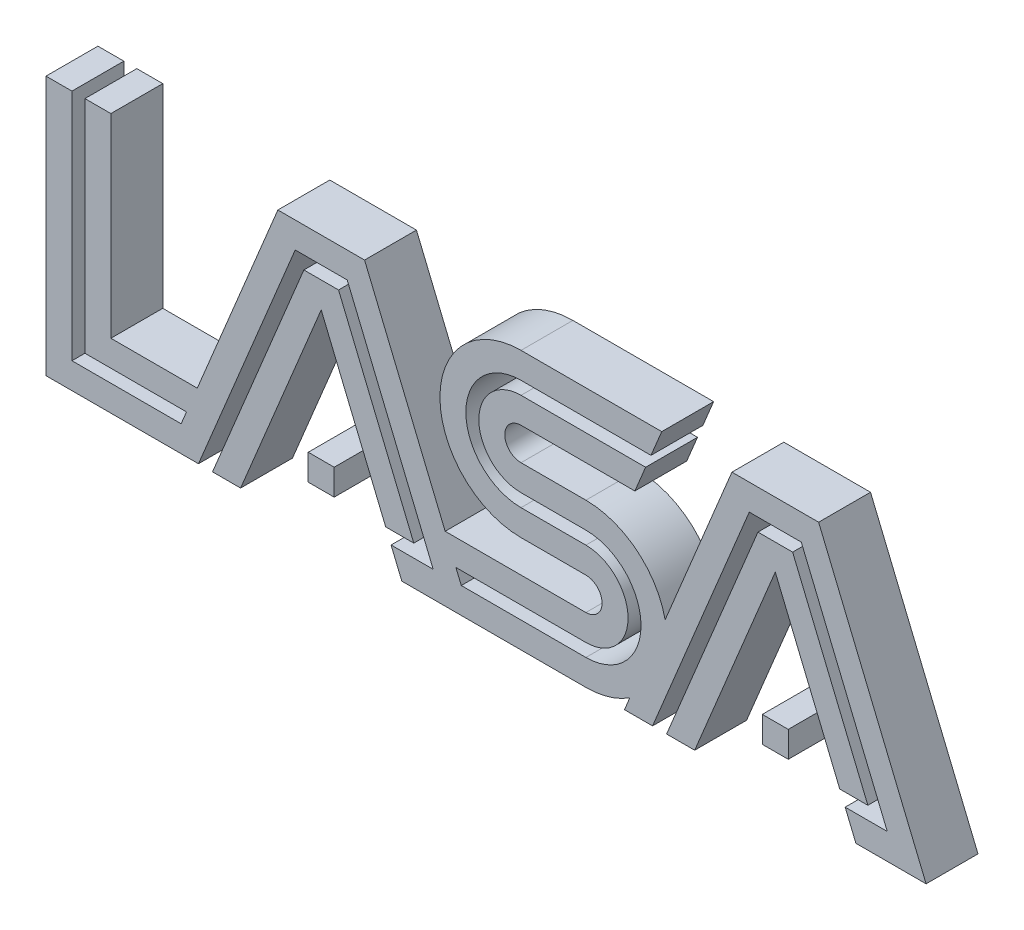
SolidWorks part; units mm, degrees
ref_plane "Front Plane" through (0, 0, 0) normal (0, 0, 1) x (1, 0, 0)
ref_plane "Top Plane" through (0, 0, 0) normal (0, 1, 0) x (1, 0, 0)
ref_plane "Right Plane" through (0, 0, 0) normal (1, 0, 0) x (0, 0, -1)
sketch "Sketch2" plane through (0, 0, 0) normal (0, 0, 1) x (1, 0, 0)
  line L0 (0, 0) -> (0, 100)
  line L1 (0, 100) -> (25, 100)
  line L2 (25, 100) -> (25, 25)
  line L3 (25, 25) -> (58.2955, 25)
  line L4 (0, 0) -> (75, 0)
  line L5 (25, 25) -> (25, 0) construction
  line L6 (58.2955, 25) -> (89.3616, 100)
  line L7 (89.3616, 100) -> (122.7705, 100)
  line L8 (122.7705, 100) -> (153.8365, 25)
  line L9 (75, 0) -> (106.066, 75)
  line L10 (106.066, 75) -> (137.132, 0)
  line L11 (58.2955, 25) -> (81.3925, 15.4329) construction
  line L12 (153.8365, 25) -> (130.7395, 15.4329) construction
  line L13 (106.066, 75) -> (106.066, 100) construction
  line L14 (137.132, 0) -> (208.0693, 0)
  line L15 (153.8365, 25) -> (208.0693, 25)
  line L16 (208.0693, 37.5) -> (183.0693, 37.5)
  line L17 (208.0693, 62.5) -> (183.0693, 62.5)
  line L18 (183.0693, 75) -> (226.9464, 75)
  line L19 (183.0693, 100) -> (237.3017, 100)
  line L20 (225.0062, 4.9878) -> (222.9402, 0)
  line L21 (222.9402, 0) -> (250, 0)
  line L22 (250, 0) -> (281.066, 75)
  line L23 (238.6157, 37.844) -> (264.3616, 100)
  line L24 (238.6157, 37.844) -> (261.7127, 28.2769) construction
  line L25 (142.6496, 52.0076) -> (154.1981, 56.7911) construction
  line L26 (264.3616, 100) -> (297.7705, 100)
  line L27 (281.066, 75) -> (281.066, 100) construction
  line L28 (281.066, 75) -> (312.132, 0)
  line L29 (312.132, 0) -> (339.1918, 0)
  line L30 (339.1918, 0) -> (297.7705, 100)
  line L31 (312.132, 0) -> (335.229, 9.5671) construction
  line L32 (183.0693, 75) -> (183.0693, 62.5) construction
  line L33 (237.3017, 100) -> (226.9464, 75)
  line L34 (226.9464, 75) -> (250.0434, 65.4329) construction
  line L35 (106.066, 75) -> (106.066, 20) construction
  line L36 (281.066, 75) -> (281.066, 20) construction
  line L37 (111.066, 15) -> (101.066, 15)
  line L38 (111.066, 15) -> (111.066, 25)
  line L39 (111.066, 25) -> (101.066, 25)
  line L40 (101.066, 15) -> (101.066, 25)
  line L41 (111.066, 15) -> (101.066, 25) construction
  line L42 (111.066, 25) -> (101.066, 15) construction
  line L44 (276.066, 15) -> (286.066, 15)
  line L45 (276.066, 15) -> (276.066, 25)
  line L46 (276.066, 25) -> (286.066, 25)
  line L47 (286.066, 15) -> (286.066, 25)
  line L48 (276.066, 15) -> (286.066, 25) construction
  line L49 (276.066, 25) -> (286.066, 15) construction
  arc A0 (208.0693, 25) -> (208.0693, 37.5) centre (208.0693, 31.25) ccw
  arc A1 (208.0693, 0) -> (208.0693, 62.5) centre (208.0693, 31.25) ccw construction
  arc A2 (183.0693, 62.5) -> (183.0693, 75) centre (183.0693, 68.75) cw
  arc A3 (183.0693, 37.5) -> (183.0693, 100) centre (183.0693, 68.75) cw
  arc A4 (208.0693, 0) -> (225.0062, 4.9878) centre (208.0693, 31.25) ccw
  arc A5 (208.0693, 62.5) -> (238.6157, 37.844) centre (208.0693, 31.25) cw
  dimension "D6" = 10
  dimension "D1" = 100
  dimension "D2" = 25
  dimension "D3" = 45
  dimension "D4" = 75
  dimension "D5" = 175
extrude "Boss-Extrude1" add sketch "Sketch2" along normal blind 20 contours L1 L2 L3 L6 L7 L8 L15 A0 L16 A3 L19 L33 L18 A2 L17 A5 L23 L26 L30 L29 L28 L22 L21 L20 A4 L14 L10 L9 L4 L0 | L37 L40 L39 L38 | L44 L47 L46 L45
sketch "Sketch5" plane through (0, 0, 20) normal (0, 0, 1) x (1, 0, 0)
  line L0 (10, 100) -> (10, 10)
  line L1 (0, 100) -> (25, 100) construction
  line L2 (10, 10) -> (52.0823, 10)
  line L3 (52.0823, 10) -> (54.1534, 15)
  line L4 (54.1534, 15) -> (15, 15)
  line L5 (15, 15) -> (15, 100)
  line L6 (15, 100) -> (10, 100)
  line L7 (0, 100) -> (10, 100) construction
  line L8 (15, 100) -> (25, 100) construction
  line L9 (25, 25) -> (25, 15) construction
  line L10 (25, 10) -> (25, 0) construction
  line L11 (0, 0) -> (75, 0) construction
  line L12 (58.2955, 25) -> (89.3616, 100) construction
  line L13 (64.1761, 0) -> (99.3842, 85)
  line L14 (99.3842, 85) -> (112.7478, 85)
  line L15 (112.7478, 85) -> (141.7428, 15)
  line L16 (141.7428, 15) -> (130.9188, 15)
  line L17 (106.066, 75) -> (137.132, 0) construction
  line L18 (130.9188, 15) -> (132.9899, 10)
  line L19 (132.9899, 10) -> (149.2258, 10)
  line L20 (149.2258, 10) -> (116.0887, 90)
  line L21 (116.0887, 90) -> (96.0433, 90)
  line L22 (96.0433, 90) -> (58.7641, 0)
  line L23 (58.7641, 0) -> (64.1761, 0)
  line L24 (122.7705, 100) -> (153.8365, 25) construction
  line L25 (96.0433, 90) -> (86.8045, 93.8268) construction
  line L26 (106.066, 90) -> (106.066, 100) construction
  line L27 (89.3616, 100) -> (122.7705, 100) construction
  line L28 (106.066, 75) -> (96.8272, 78.8268) construction
  line L29 (106.066, 75) -> (115.3048, 78.8268) construction
  line L30 (106.066, 85) -> (106.066, 75) construction
  line L31 (149.2258, 10) -> (149.2258, 0) construction
  line L32 (137.132, 0) -> (208.0693, 0) construction
  line L33 (141.7428, 15) -> (141.7428, 10) construction
  line L34 (231.0885, 85) -> (233.1596, 90)
  line L35 (237.3017, 100) -> (226.9464, 75) construction
  line L36 (233.1596, 90) -> (183.0693, 90)
  line L37 (231.0885, 85) -> (183.0693, 85)
  line L38 (183.0693, 52.5) -> (208.0693, 52.5)
  line L39 (183.0693, 47.5) -> (208.0693, 47.5)
  line L40 (208.0693, 15) -> (157.9786, 15)
  line L41 (157.9786, 15) -> (160.0497, 10)
  line L42 (160.0497, 10) -> (208.0693, 10)
  line L43 (239.1761, 0) -> (233.7641, 0)
  line L44 (222.9402, 0) -> (250, 0) construction
  line L45 (233.7641, 0) -> (271.0433, 90)
  line L46 (271.0433, 90) -> (291.0887, 90)
  line L47 (291.0887, 90) -> (324.2258, 10)
  line L48 (324.2258, 10) -> (307.9899, 10)
  line L49 (281.066, 75) -> (312.132, 0) construction
  line L50 (307.9899, 10) -> (305.9188, 15)
  line L51 (305.9188, 15) -> (316.7428, 15)
  line L52 (316.7428, 15) -> (287.7478, 85)
  line L53 (287.7478, 85) -> (274.3842, 85)
  line L54 (274.3842, 85) -> (239.1761, 0)
  line L56 (250, 0) -> (281.066, 75) construction
  line L57 (281.066, 90) -> (281.066, 100) construction
  line L58 (264.3616, 100) -> (297.7705, 100) construction
  line L59 (281.066, 85) -> (281.066, 90) construction
  arc A0 (183.0693, 85) -> (183.0693, 52.5) centre (183.0693, 68.75) ccw
  arc A1 (183.0693, 90) -> (183.0693, 47.5) centre (183.0693, 68.75) ccw
  arc A2 (208.0693, 47.5) -> (208.0693, 15) centre (208.0693, 31.25) cw
  arc A3 (208.0693, 52.5) -> (208.0693, 10) centre (208.0693, 31.25) cw
  dimension "D1" = 5
extrude "Cut-Extrude1" cut sketch "Sketch5" against normal through all
ref_plane "FloorPlane" through (0, 0, 0) normal (0, -1, 0) x (-1, 0, 0)
